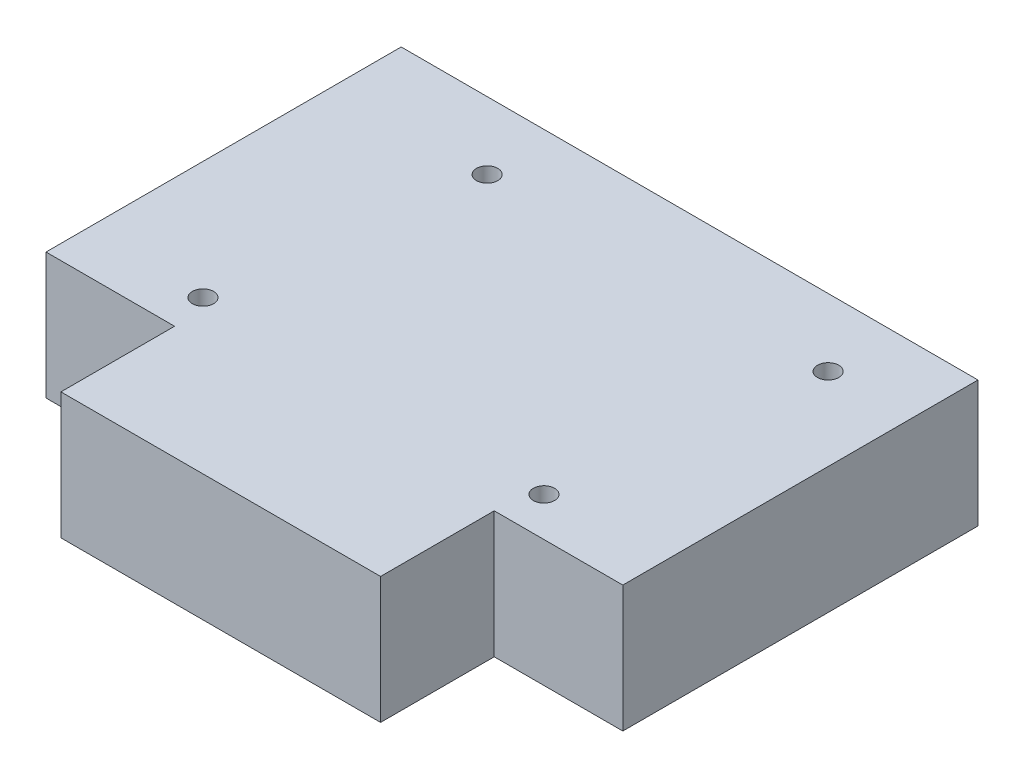
SolidWorks part; units mm, degrees
ref_plane "Front Plane" through (0, 0, 0) normal (0, 0, 1) x (1, 0, 0)
ref_plane "Top Plane" through (0, 0, 0) normal (0, 1, 0) x (1, 0, 0)
ref_plane "Right Plane" through (0, 0, 0) normal (1, 0, 0) x (0, 0, -1)
sketch "Sketch1" plane through (0, 0, 0) normal (0, 1, 0) x (1, 0, 0)
  line L0 (-22.5, -25) -> (22.5, -25) construction
  line L1 (-40.6, -25) -> (-22.5, -25)
  line L2 (-40.6, -25) -> (-40.6, 25)
  line L3 (-40.6, 25) -> (40.6, 25)
  line L4 (40.6, -25) -> (40.6, 25)
  line L5 (-40.6, -25) -> (40.6, 25) construction
  line L6 (-40.6, 25) -> (40.6, -25) construction
  line L7 (-22.5, -25) -> (22.5, -25) construction
  line L8 (-22.5, -25) -> (-22.5, -41)
  line L9 (-22.5, -41) -> (22.5, -41)
  line L10 (22.5, -25) -> (22.5, -41)
  line L11 (22.5, -25) -> (40.6, -25)
  circle A0 centre (-19, 15.5) radius 1.5
  circle A1 centre (29, 15.5) radius 1.5
  circle A2 centre (-24, -19.5) radius 1.5
  circle A3 centre (24, -19.5) radius 1.5
  point P0 (0, 0)
  point P10 (0, -41)
  dimension "D5" = 3
  dimension "D1" = 81.2
  dimension "D2" = 50
  dimension "D3" = 66
  dimension "D4" = 45
  dimension "D6" = 48
  dimension "D7" = 48
  dimension "D8" = 5.5
  dimension "D9" = 16.6
  dimension "D10" = 5
  dimension "D11" = 35
extrude "Boss-Extrude1" add sketch "Sketch1" along normal blind 17.8
